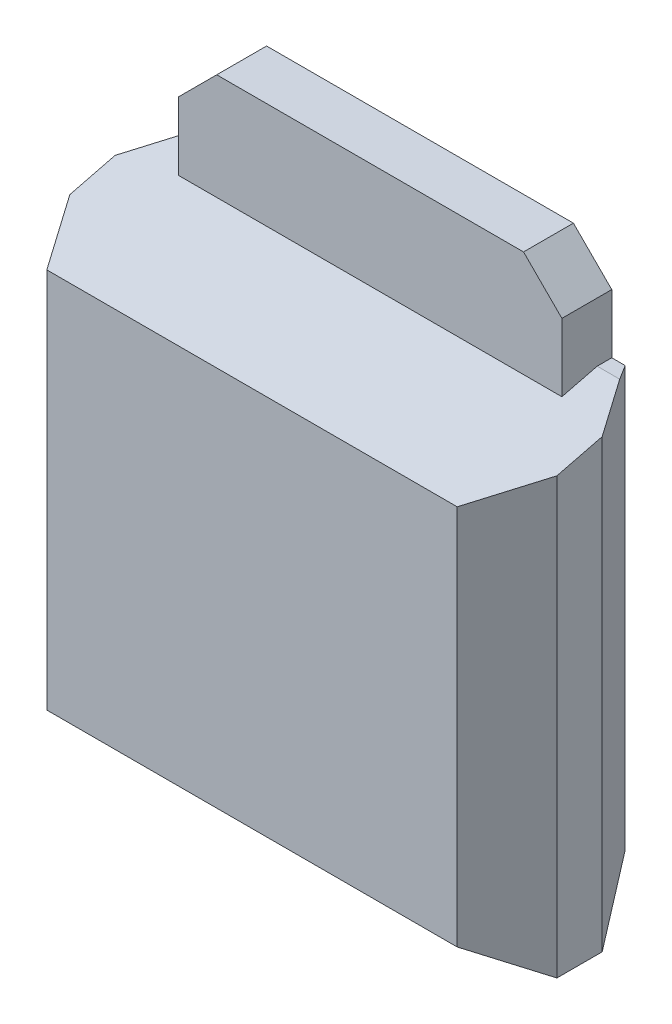
SolidWorks part; units mm, degrees
ref_plane "Plan de face" through (0, 0, 0) normal (0, 0, 1) x (1, 0, 0)
ref_plane "Plan de dessus" through (0, 0, 0) normal (0, 1, 0) x (1, 0, 0)
ref_plane "Plan de droite" through (0, 0, 0) normal (1, 0, 0) x (0, 0, -1)
sketch "Esquisse1" plane through (0, 0, 0) normal (0, 0, 1) x (1, 0, 0)
  line L1 (0, 0) -> (6.35, 0)
  line L2 (0, 0) -> (0, 5.97)
  line L3 (0, 5.97) -> (6.35, 5.97)
  line L4 (6.35, 0) -> (6.35, 5.97)
extrude "Boss.-Extru.1" add sketch "Esquisse1" along normal blind 2.19
chamfer "Chanfrein1" distance 0.8 distance2 0.5 1 edges at (6.35, 2.985, 2.19)
chamfer "Chanfrein2" distance 0.5 distance2 0.8 1 edges at (6.35, 2.985, 0)
chamfer "Chanfrein3" distance 0.8 distance2 0.5 1 edges at (2.925, 0, 2.19)
chamfer "Chanfrein4" distance 0.5 distance2 0.8 1 edges at (2.925, 0, 0)
chamfer "Chanfrein5" distance 0.8 distance2 0.5 1 edges at (0, 3.235, 2.19)
chamfer "Chanfrein6" distance 0.5 distance2 0.8 1 edges at (0, 3.235, 0)
chamfer "Chanfrein7" distance 2 distance2 0.5 1 edges at (3.175, 5.97, 2.19)
sketch "Esquisse2" plane through (0, 5.97, 0) normal (0, 1, 0) x (-1, 0, 0)
  line L0 (-3.175, 0) -> (-3.175, 2.5222) construction
  line L1 (-5.85, 0) -> (-0.5, 0) construction
  line L2 (-0.675, 0) -> (-0.675, 0.65)
  line L3 (-5.675, 0) -> (-5.675, 0.65)
  line L4 (-0.675, 0) -> (-5.675, 0)
  line L5 (-0.675, 0.65) -> (-5.675, 0.65)
  line L7 (-0.675, 0) -> (-0.675, 2.5222) construction
  line L8 (-5.675, 0) -> (-5.675, 2.5222) construction
  dimension "D1" = 2.5
  dimension "D3" = 0.65
  dimension "D2" = 2.5
extrude "Boss.-Extru.2" add sketch "Esquisse2" along normal blind 1.27 and the other way blind 5
chamfer "Chanfrein8" distance 0.5 angle 45 2 edges at (5.675, 7.24, 0.325) (0.675, 7.24, 0.325)
